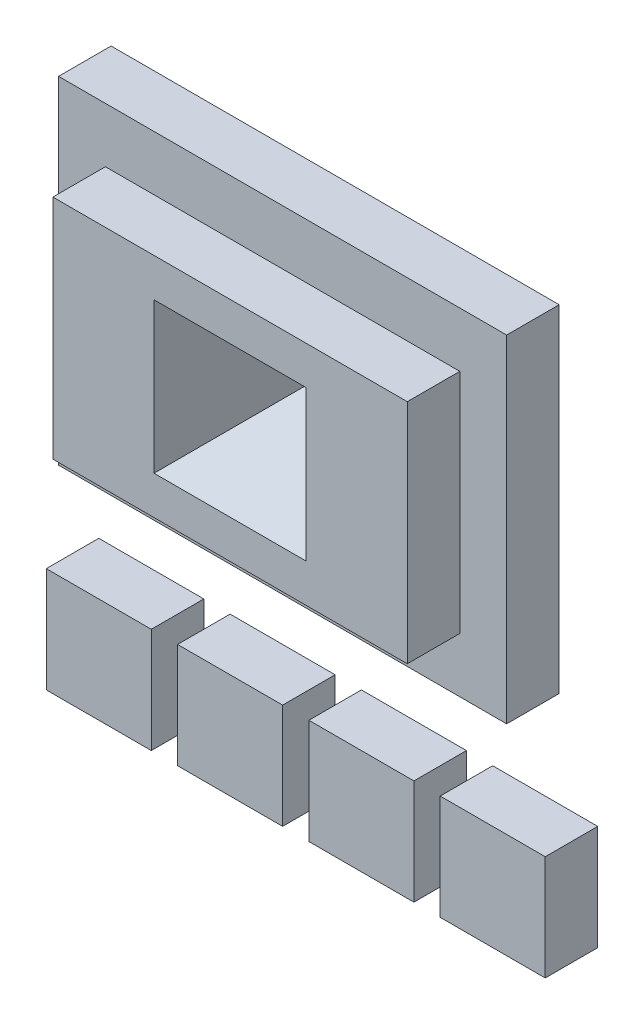
SolidWorks part; units mm, degrees
ref_plane "Front Plane" through (0, 0, 0) normal (0, 0, 1) x (1, 0, 0)
ref_plane "Top Plane" through (0, 0, 0) normal (0, 1, 0) x (1, 0, 0)
ref_plane "Right Plane" through (0, 0, 0) normal (1, 0, 0) x (0, 0, -1)
sketch "Sketch1" plane through (0, 0, 0) normal (0, 0, 1) x (1, 0, 0)
  line L0 (15, 10) -> (35, 10)
  line L1 (-10, 10) -> (10, 10)
  line L2 (-10, 10) -> (-10, -10)
  line L3 (-10, -10) -> (10, -10)
  line L4 (10, 10) -> (10, -10)
  line L5 (-10, 10) -> (10, -10) construction
  line L6 (-10, -10) -> (10, 10) construction
  line L7 (15, 10) -> (15, -10)
  line L8 (15, -10) -> (35, -10)
  line L9 (35, 10) -> (35, -10)
  line L10 (15, 10) -> (35, -10) construction
  line L11 (15, -10) -> (35, 10) construction
  line L12 (40, 10) -> (60, 10)
  line L13 (40, 10) -> (40, -10)
  line L14 (40, -10) -> (60, -10)
  line L15 (60, 10) -> (60, -10)
  line L16 (40, 10) -> (60, -10) construction
  line L17 (40, -10) -> (60, 10) construction
  line L18 (65, 10) -> (85, 10)
  line L19 (65, 10) -> (65, -10)
  line L20 (65, -10) -> (85, -10)
  line L21 (85, 10) -> (85, -10)
  line L22 (65, 10) -> (85, -10) construction
  line L23 (65, -10) -> (85, 10) construction
  line L25 (-7.6562, 92.3452) -> (77.6562, 92.3452)
  line L26 (-7.6562, 92.3452) -> (-7.6562, 28.2316)
  line L27 (-7.6562, 28.2316) -> (77.6562, 28.2316)
  line L28 (77.6562, 92.3452) -> (77.6562, 28.2316)
  line L29 (-7.6562, 92.3452) -> (77.6562, 28.2316) construction
  line L30 (-7.6562, 28.2316) -> (77.6562, 92.3452) construction
  point P0 (0, 0)
  point P6 (35, 60.2884)
  point P7 (25, 0)
  point P12 (50, 0)
  point P17 (75, 0)
  dimension "D1" = 20
  dimension "D2" = 20
  dimension "D3" = 4
extrude "Boss-Extrude1" add sketch "Sketch1" along normal blind 10
sketch "Sketch4" plane through (0, 0, 10) normal (0, 0, 1) x (1, 0, 0)
  line L1 (1.2618, 81.8985) -> (68.7382, 81.8985)
  line L2 (1.2618, 81.8985) -> (1.2618, 38.6782)
  line L3 (1.2618, 38.6782) -> (68.7382, 38.6782)
  line L4 (68.7382, 81.8985) -> (68.7382, 38.6782)
  line L5 (1.2618, 81.8985) -> (68.7382, 38.6782) construction
  line L6 (1.2618, 38.6782) -> (68.7382, 81.8985) construction
  point P0 (35, 60.2884)
extrude "Boss-Extrude2" add sketch "Sketch4" along normal blind 10
sketch "Sketch5" plane through (0, 0, 20) normal (0, 0, 1) x (1, 0, 0)
  line L1 (20.5148, 74.5905) -> (49.4852, 74.5905)
  line L2 (20.5148, 74.5905) -> (20.5148, 45.9863)
  line L3 (20.5148, 45.9863) -> (49.4852, 45.9863)
  line L4 (49.4852, 74.5905) -> (49.4852, 45.9863)
  line L5 (20.5148, 74.5905) -> (49.4852, 45.9863) construction
  line L6 (20.5148, 45.9863) -> (49.4852, 74.5905) construction
  point P0 (35, 60.2884)
extrude "Cut-Extrude1" cut sketch "Sketch5" against normal blind 20 draft 25
